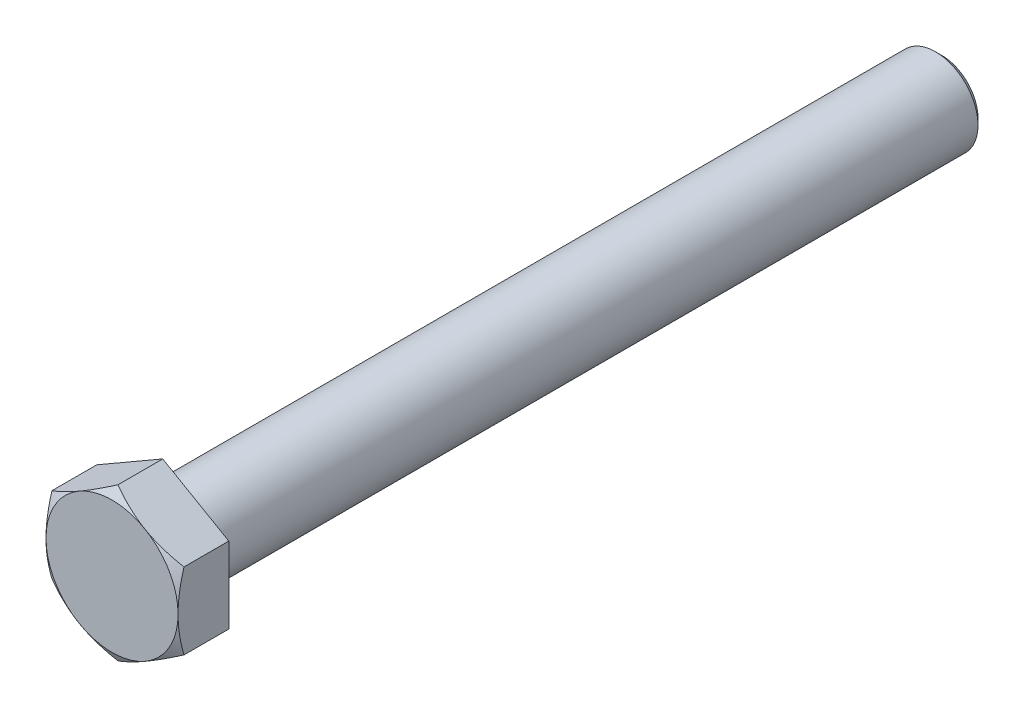
SolidWorks part; units mm, degrees
ref_plane "Front Plane" through (0, 0, 0) normal (0, 0, 1) x (1, 0, 0)
ref_plane "Top Plane" through (0, 0, 0) normal (0, 1, 0) x (1, 0, 0)
ref_plane "Right Plane" through (0, 0, 0) normal (1, 0, 0) x (0, 0, -1)
sketch "Sketch1" plane through (0, 0, 0) normal (0, 0, 1) x (1, 0, 0)
  line L0 (0, 0) -> (0, 10.7791) construction
  line L2 (0, 10.7791) -> (-9.335, 5.3896)
  line L3 (-9.335, 5.3896) -> (-9.335, -5.3896)
  line L4 (-9.335, -5.3896) -> (0, -10.7791)
  line L5 (0, -10.7791) -> (9.335, -5.3896)
  line L6 (9.335, -5.3896) -> (9.335, 5.3896)
  line L7 (9.335, 5.3896) -> (0, 10.7791)
  circle A0 centre (0, 0) radius 9.335 construction
  dimension "HEX" = 18.67
extrude "Boss-Extrude1" add sketch "Sketch1" along normal blind 7.32
sketch "Sketch2" plane through (0, 0, 0) normal (1, 0, 0) x (0, 0, -1)
  line L0 (0, 0) -> (110, 0) construction
  line L1 (0, 0) -> (0, 6.6)
  line L4 (109.1, 6) -> (110, 5.1)
  line L7 (110, 5.1) -> (110, 0)
  line L8 (110, 0) -> (0, 0)
  line L9 (109.1, 6) -> (0.6, 6)
  arc A3 (0.6, 6) -> (0, 6.6) centre (0.6, 6.6) cw
  dimension "D1" = 0.6
  dimension "LENGTH" = 110
  dimension "WIDTH2" = 10.2
  dimension "WIDTH1" = 12
  dimension "D5" = 45
revolve "Revolve1" add sketch "Sketch2" angle 360 about L0
cosmetic thread "Cosmetic Thread1" parameters "D1"=30, "D2"=12
sketch "Sketch3" plane through (0, 0, 0) normal (1, 0, 0) x (0, 0, -1)
  line L0 (-12.2049, 0) -> (129.7862, 0) construction
  line L1 (-7.32, 10.7791) -> (-6.4862, 10.7791)
  line L2 (-0.15, 10.7791) -> (-0.15, 8.7866)
  line L3 (-6.4862, 10.7791) -> (-7.32, 9.335)
  line L4 (-0.15, 8.7866) -> (0, 8.7)
  line L5 (-7.32, 9.335) -> (-7.32, 10.7791)
  line L6 (0, -5.3896) -> (0, 5.3896) construction
  line L7 (-7.32, 10.7791) -> (0, 10.7791) construction
  line L8 (-7.32, 5.3896) -> (-7.32, 10.7791) construction
  line L10 (0, 8.7) -> (0, 10.7791)
  line L11 (0, 10.7791) -> (-0.15, 10.7791)
  dimension "D1" = 30
  dimension "SAME AS HEX" = 18.67
  dimension "D3" = 30
  dimension "C" = 0.15
  dimension "DW" = 17.4
revolve "Cut-Revolve1" cut sketch "Sketch3" angle 360 about L0
